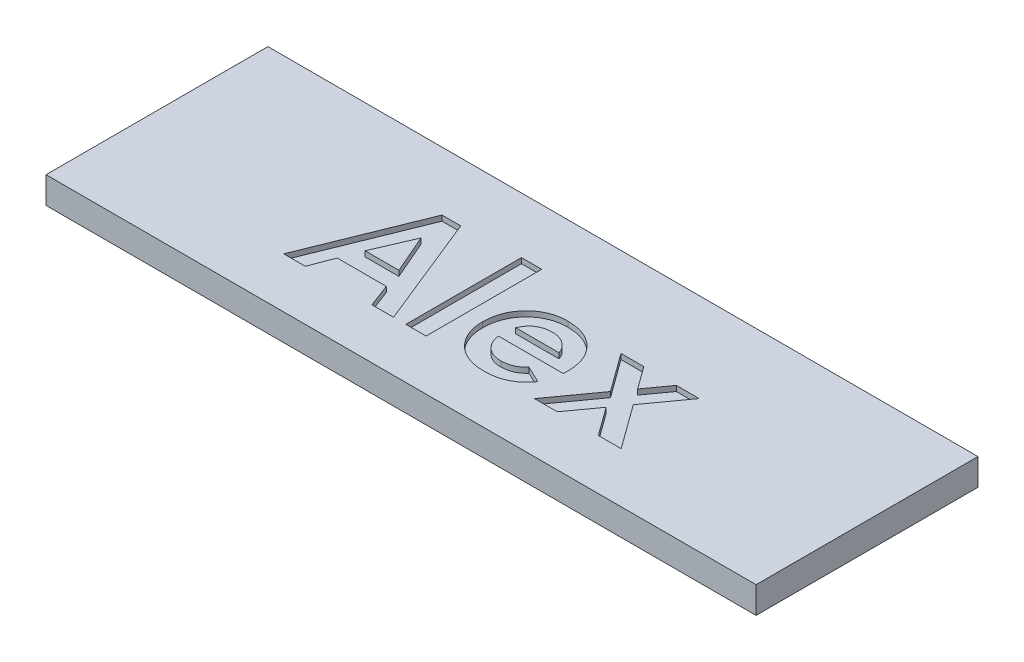
SolidWorks part; units mm, degrees
ref_plane "Front Plane" through (0, 0, 0) normal (0, 0, 1) x (1, 0, 0)
ref_plane "Top Plane" through (0, 0, 0) normal (0, 1, 0) x (1, 0, 0)
ref_plane "Right Plane" through (0, 0, 0) normal (1, 0, 0) x (0, 0, -1)
sketch "Sketch1" plane through (0, 0, 0) normal (0, 1, 0) x (1, 0, 0)
  line L0 (-18.0359, -28.097) -> (61.9641, -28.097) construction
  line L1 (-18.0359, -28.097) -> (61.9641, -28.097)
  line L2 (-18.0359, -28.097) -> (-18.0359, -3.097)
  line L3 (-18.0359, -3.097) -> (61.9641, -3.097)
  line L4 (61.9641, -28.097) -> (61.9641, -3.097)
  line L5 (-18.0359, -28.097) -> (61.9641, -3.097) construction
  line L6 (-18.0359, -3.097) -> (61.9641, -28.097) construction
  line L7 (-18.0359, -3.097) -> (-18.0359, -28.097) construction
  point P0 (21.9641, -15.597)
extrude "Boss-Extrude1" add sketch "Sketch1" along normal blind 3
sketch "Sketch2" plane through (0, 0, 0) normal (0, -1, 0) x (1, 0, 0)
  circle A0 centre (-14.6216, 24.6828) radius 2.25
  circle A1 centre (-14.6216, 6.5112) radius 2.25
  circle A2 centre (54.5499, 24.6828) radius 2.25
  circle A3 centre (54.5499, 6.5112) radius 2.25
  dimension "D1" = 4.5
extrude "Cut-Extrude1" cut sketch "Sketch2" against normal blind 1.5
sketch "Sketch3" plane through (0, 3, 0) normal (0, 1, 0) x (1, 0, 0)
  line L0 (-14.1657, -22.4277) -> (58.0939, -22.4277) construction
  line L1 (-18.0359, -28.097) -> (61.9641, -28.097) construction
  text T0 "Alex" font "Century Gothic" height in points 48
  point P2 (21.9641, -28.097)
  point P3 (21.9641, -22.4277)
extrude "Cut-Extrude2" cut sketch "Sketch3" against normal blind 0.6
